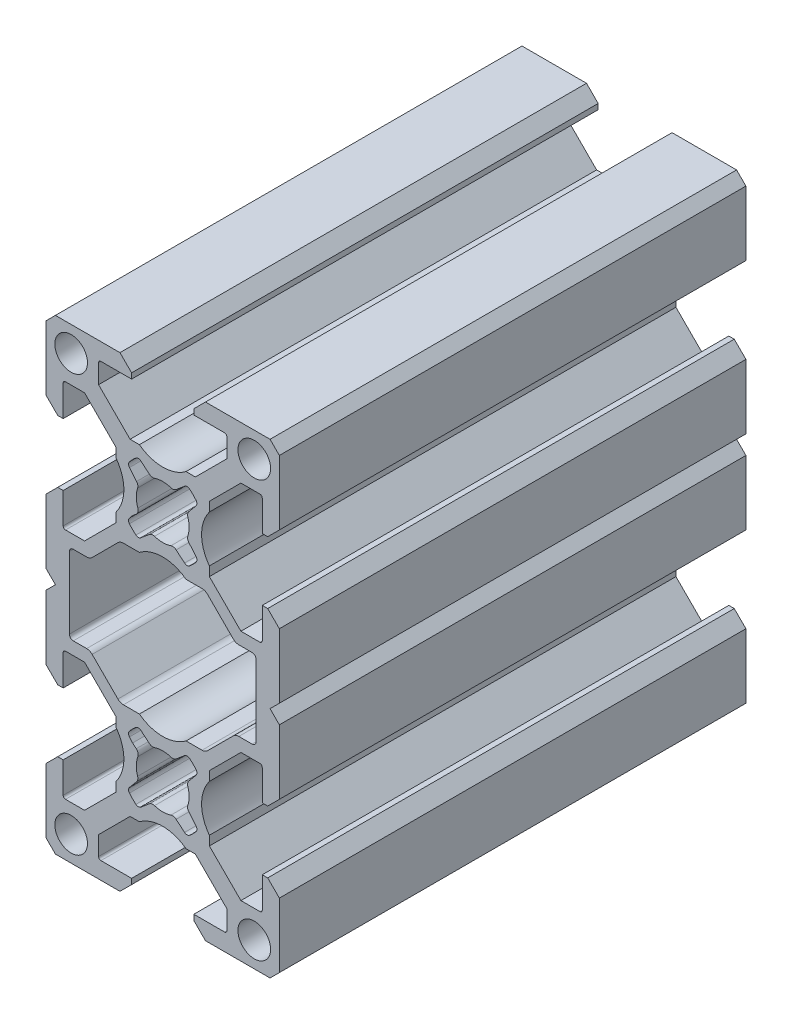
SolidWorks part; units mm, degrees
material "1060-H12"
ref_plane "Спереди" through (0, 0, 0) normal (0, 0, 1) x (1, 0, 0)
ref_plane "Сверху" through (0, 0, 0) normal (0, 1, 0) x (1, 0, 0)
ref_plane "Сбоку" through (0, 0, 0) normal (1, 0, 0) x (0, 0, -1)
sketch "Model" plane through (0, 0, 0) normal (0, 0, 1) x (1, 0, 0)
  line L0 (-6, 19.1969) -> (-6, 15.866)
  line L1 (-10.0531, 6.75) -> (-6, 10.8031)
  line L2 (-12.5, 6.75) -> (-10.0531, 6.75)
  line L3 (-12.8, 11) -> (-12.8, 7.05)
  line L4 (-14.5, 11) -> (-12.8, 11)
  line L5 (-14.5, 10.5) -> (-14.5, 11)
  line L6 (-15, 10.5) -> (-14.5, 10.5)
  line L7 (-1.8557, 11.5271) -> (-2.8145, 10.7226)
  line L8 (-4.2774, 12.1855) -> (-3.4729, 13.1443)
  line L9 (-10.0531, 23.25) -> (-6, 19.1969)
  line L10 (-12.5, 23.25) -> (-10.0531, 23.25)
  line L11 (-12.8, 19) -> (-12.8, 22.95)
  line L12 (-14.5, 19) -> (-12.8, 19)
  line L13 (-14.5, 19.5) -> (-14.5, 19)
  line L14 (-15, 19.5) -> (-14.5, 19.5)
  line L15 (-15, 30) -> (-15, 19.5)
  line L20 (-4.5, 30) -> (-15, 30)
  line L21 (12.8, 19) -> (12.8, 22.95)
  line L22 (14.5, 19) -> (12.8, 19)
  line L23 (14.5, 19.5) -> (14.5, 19)
  line L24 (15, 19.5) -> (14.5, 19.5)
  line L25 (15, 30) -> (15, 19.5)
  line L30 (12.8, 11) -> (12.8, 7.05)
  line L31 (14.5, 11) -> (12.8, 11)
  line L32 (14.5, 10.5) -> (14.5, 11)
  line L33 (15, 10.5) -> (14.5, 10.5)
  line L34 (4.5, 30) -> (15, 30)
  line L35 (-4, 27.8) -> (-7.95, 27.8)
  line L36 (-4, 29.5) -> (-4, 27.8)
  line L37 (-4.5, 29.5) -> (-4, 29.5)
  line L38 (-4.5, 30) -> (-4.5, 29.5)
  line L39 (4, 27.8) -> (7.95, 27.8)
  line L40 (4, 29.5) -> (4, 27.8)
  line L41 (4.5, 29.5) -> (4, 29.5)
  line L42 (4.5, 30) -> (4.5, 29.5)
  line L43 (-1.8557, 18.4729) -> (-2.8145, 19.2774)
  line L44 (-4.2774, 17.8145) -> (-3.4729, 16.8557)
  line L45 (1.8557, 11.5271) -> (2.8145, 10.7226)
  line L46 (4.2774, 12.1855) -> (3.4729, 13.1443)
  line L47 (1.8557, 18.4729) -> (2.8145, 19.2774)
  line L48 (4.2774, 17.8145) -> (3.4729, 16.8557)
  line L49 (-5.5, 15) -> (-6, 15.866)
  line L50 (-6, 14.134) -> (-6, 10.8031)
  line L51 (-5.5, 15) -> (-6, 14.134)
  line L52 (9.0768, 5.3929) -> (5.7626, 8.7071)
  line L53 (-5.0555, 9) -> (5.0555, 9)
  line L54 (-9.0768, 5.3929) -> (-5.7626, 8.7071)
  line L55 (-8.25, 25.0531) -> (-4.1969, 21)
  line L56 (-8.25, 27.5) -> (-8.25, 25.0531)
  line L57 (4.1969, 21) -> (0.866, 21)
  line L58 (8.25, 25.0531) -> (4.1969, 21)
  line L59 (0, 20.5) -> (0.866, 21)
  line L60 (-0.866, 21) -> (-4.1969, 21)
  line L61 (0, 20.5) -> (-0.866, 21)
  line L62 (8.25, 27.5) -> (8.25, 25.0531)
  line L63 (10.0531, 23.25) -> (6, 19.1969)
  line L64 (12.5, 23.25) -> (10.0531, 23.25)
  line L65 (6, 10.8031) -> (6, 14.134)
  line L66 (10.0531, 6.75) -> (6, 10.8031)
  line L67 (5.5, 15) -> (6, 14.134)
  line L68 (6, 15.866) -> (6, 19.1969)
  line L69 (5.5, 15) -> (6, 15.866)
  line L70 (12.5, 6.75) -> (10.0531, 6.75)
  line L71 (-6, -19.1969) -> (-6, -15.866)
  line L72 (-10.0531, -23.25) -> (-6, -19.1969)
  line L73 (-12.5, -23.25) -> (-10.0531, -23.25)
  line L74 (-12.8, -19) -> (-12.8, -22.95)
  line L75 (-14.5, -19) -> (-12.8, -19)
  line L76 (-14.5, -19.5) -> (-14.5, -19)
  line L77 (-15, -19.5) -> (-14.5, -19.5)
  line L78 (-15, -30) -> (-15, -19.5)
  line L83 (-4.5, -30) -> (-15, -30)
  line L84 (12.8, -19) -> (12.8, -22.95)
  line L85 (14.5, -19) -> (12.8, -19)
  line L86 (14.5, -19.5) -> (14.5, -19)
  line L87 (15, -19.5) -> (14.5, -19.5)
  line L88 (15, -30) -> (15, -19.5)
  line L93 (4.5, -30) -> (15, -30)
  line L94 (-4, -27.8) -> (-7.95, -27.8)
  line L95 (-4, -29.5) -> (-4, -27.8)
  line L96 (-4.5, -29.5) -> (-4, -29.5)
  line L97 (-4.5, -30) -> (-4.5, -29.5)
  line L98 (4, -27.8) -> (7.95, -27.8)
  line L99 (4, -29.5) -> (4, -27.8)
  line L100 (4.5, -29.5) -> (4, -29.5)
  line L101 (4.5, -30) -> (4.5, -29.5)
  line L102 (-1.8557, -18.4729) -> (-2.8145, -19.2774)
  line L103 (-4.2774, -17.8145) -> (-3.4729, -16.8557)
  line L104 (1.8557, -18.4729) -> (2.8145, -19.2774)
  line L105 (4.2774, -17.8145) -> (3.4729, -16.8557)
  line L106 (-5.5, -15) -> (-6, -15.866)
  line L107 (-5.5, -15) -> (-6, -14.134)
  line L108 (-8.25, -25.0531) -> (-4.1969, -21)
  line L109 (-8.25, -27.5) -> (-8.25, -25.0531)
  line L110 (4.1969, -21) -> (0.866, -21)
  line L111 (8.25, -25.0531) -> (4.1969, -21)
  line L112 (0, -20.5) -> (0.866, -21)
  line L113 (-0.866, -21) -> (-4.1969, -21)
  line L114 (0, -20.5) -> (-0.866, -21)
  line L115 (8.25, -27.5) -> (8.25, -25.0531)
  line L116 (10.0531, -23.25) -> (6, -19.1969)
  line L117 (12.5, -23.25) -> (10.0531, -23.25)
  line L118 (5.5, -15) -> (6, -14.134)
  line L119 (6, -15.866) -> (6, -19.1969)
  line L120 (5.5, -15) -> (6, -15.866)
  line L121 (-10.0531, -6.75) -> (-6, -10.8031)
  line L122 (-12.5, -6.75) -> (-10.0531, -6.75)
  line L123 (-12.8, -11) -> (-12.8, -7.05)
  line L124 (-14.5, -11) -> (-12.8, -11)
  line L125 (-14.5, -10.5) -> (-14.5, -11)
  line L126 (-15, -10.5) -> (-14.5, -10.5)
  line L127 (-6, -14.134) -> (-6, -10.8031)
  line L128 (-15, 10.5) -> (-15, -10.5)
  line L129 (-1.8557, -11.5271) -> (-2.8145, -10.7226)
  line L130 (-4.2774, -12.1855) -> (-3.4729, -13.1443)
  line L131 (1.8557, -11.5271) -> (2.8145, -10.7226)
  line L132 (4.2774, -12.1855) -> (3.4729, -13.1443)
  line L133 (6, -10.8031) -> (6, -14.134)
  line L134 (10.0531, -6.75) -> (6, -10.8031)
  line L135 (12.8, -11) -> (12.8, -7.05)
  line L136 (14.5, -11) -> (12.8, -11)
  line L137 (14.5, -10.5) -> (14.5, -11)
  line L138 (15, -10.5) -> (14.5, -10.5)
  line L139 (12.5, -6.75) -> (10.0531, -6.75)
  line L140 (15, 10.5) -> (15, -10.5)
  line L141 (9.7839, 5.1) -> (12.35, 5.1)
  line L142 (-9.7839, 5.1) -> (-12.35, 5.1)
  line L143 (-13.35, 4.1) -> (-13.35, -4.1)
  line L144 (13.35, 4.1) -> (13.35, -4.1)
  line L145 (-9.0768, -5.3929) -> (-5.7626, -8.7071)
  line L146 (-9.7839, -5.1) -> (-12.35, -5.1)
  line L147 (-5.0555, -9) -> (5.0555, -9)
  line L148 (9.0768, -5.3929) -> (5.7626, -8.7071)
  line L149 (9.7839, -5.1) -> (12.35, -5.1)
  arc A0 (-3.3914, 16.3495) -> (-3.3914, 13.6505) centre (0, 15) ccw
  arc A1 (-1.3495, 11.6086) -> (1.3495, 11.6086) centre (0, 15) ccw
  arc A2 (-4.2838, 11.5505) -> (-3.4495, 10.7162) centre (0, 15) ccw
  arc A13 (-3.4729, 13.1443) -> (-3.3914, 13.6505) centre (-3.8559, 13.4657) ccw
  arc A14 (-4.2774, 12.1855) -> (-4.2838, 11.5505) centre (-3.8944, 11.8641) ccw
  arc A15 (-3.4495, 10.7162) -> (-2.8145, 10.7226) centre (-3.1359, 11.1056) ccw
  arc A16 (-1.3495, 11.6086) -> (-1.8557, 11.5271) centre (-1.5343, 11.1441) ccw
  arc A17 (-3.4495, 19.2838) -> (-4.2838, 18.4495) centre (0, 15) ccw
  arc A18 (-3.3914, 16.3495) -> (-3.4729, 16.8557) centre (-3.8559, 16.5343) ccw
  arc A19 (-4.2838, 18.4495) -> (-4.2774, 17.8145) centre (-3.8944, 18.1359) ccw
  arc A20 (-2.8145, 19.2774) -> (-3.4495, 19.2838) centre (-3.1359, 18.8944) ccw
  arc A21 (-1.8557, 18.4729) -> (-1.3495, 18.3914) centre (-1.5343, 18.8559) ccw
  arc A22 (3.3914, 13.6505) -> (3.3914, 16.3495) centre (0, 15) ccw
  arc A23 (3.4495, 10.7162) -> (4.2838, 11.5505) centre (0, 15) ccw
  arc A24 (3.3914, 13.6505) -> (3.4729, 13.1443) centre (3.8559, 13.4657) ccw
  arc A25 (4.2838, 11.5505) -> (4.2774, 12.1855) centre (3.8944, 11.8641) ccw
  arc A26 (2.8145, 10.7226) -> (3.4495, 10.7162) centre (3.1359, 11.1056) ccw
  arc A27 (1.8557, 11.5271) -> (1.3495, 11.6086) centre (1.5343, 11.1441) ccw
  arc A28 (4.2838, 18.4495) -> (3.4495, 19.2838) centre (0, 15) ccw
  arc A29 (3.4729, 16.8557) -> (3.3914, 16.3495) centre (3.8559, 16.5343) ccw
  arc A30 (4.2774, 17.8145) -> (4.2838, 18.4495) centre (3.8944, 18.1359) ccw
  arc A31 (3.4495, 19.2838) -> (2.8145, 19.2774) centre (3.1359, 18.8944) ccw
  arc A32 (1.3495, 18.3914) -> (1.8557, 18.4729) centre (1.5343, 18.8559) ccw
  arc A33 (1.3495, 18.3914) -> (-1.3495, 18.3914) centre (0, 15) ccw
  arc A34 (-12.8, 7.05) -> (-12.5, 6.75) centre (-12.5, 7.05) ccw
  arc A35 (-12.5, 23.25) -> (-12.8, 22.95) centre (-12.5, 22.95) ccw
  arc A36 (-7.95, 27.8) -> (-8.25, 27.5) centre (-7.95, 27.5) ccw
  arc A37 (8.25, 27.5) -> (7.95, 27.8) centre (7.95, 27.5) ccw
  arc A38 (12.8, 22.95) -> (12.5, 23.25) centre (12.5, 22.95) ccw
  arc A39 (12.5, 6.75) -> (12.8, 7.05) centre (12.5, 7.05) ccw
  arc A40 (-3.3914, -13.6505) -> (-3.3914, -16.3495) centre (0, -15) ccw
  arc A51 (-4.2838, -18.4495) -> (-3.4495, -19.2838) centre (0, -15) ccw
  arc A52 (-3.4729, -16.8557) -> (-3.3914, -16.3495) centre (-3.8559, -16.5343) ccw
  arc A53 (-4.2774, -17.8145) -> (-4.2838, -18.4495) centre (-3.8944, -18.1359) ccw
  arc A54 (-3.4495, -19.2838) -> (-2.8145, -19.2774) centre (-3.1359, -18.8944) ccw
  arc A55 (-1.3495, -18.3914) -> (-1.8557, -18.4729) centre (-1.5343, -18.8559) ccw
  arc A56 (3.3914, -16.3495) -> (3.3914, -13.6505) centre (0, -15) ccw
  arc A57 (3.4495, -19.2838) -> (4.2838, -18.4495) centre (0, -15) ccw
  arc A58 (3.3914, -16.3495) -> (3.4729, -16.8557) centre (3.8559, -16.5343) ccw
  arc A59 (4.2838, -18.4495) -> (4.2774, -17.8145) centre (3.8944, -18.1359) ccw
  arc A60 (2.8145, -19.2774) -> (3.4495, -19.2838) centre (3.1359, -18.8944) ccw
  arc A61 (1.8557, -18.4729) -> (1.3495, -18.3914) centre (1.5343, -18.8559) ccw
  arc A62 (-1.3495, -18.3914) -> (1.3495, -18.3914) centre (0, -15) ccw
  arc A63 (-12.8, -22.95) -> (-12.5, -23.25) centre (-12.5, -22.95) ccw
  arc A64 (-8.25, -27.5) -> (-7.95, -27.8) centre (-7.95, -27.5) ccw
  arc A65 (7.95, -27.8) -> (8.25, -27.5) centre (7.95, -27.5) ccw
  arc A66 (12.5, -23.25) -> (12.8, -22.95) centre (12.5, -22.95) ccw
  arc A67 (-4.2838, -11.5505) -> (-4.2774, -12.1855) centre (-3.8944, -11.8641) ccw
  arc A68 (-12.5, -6.75) -> (-12.8, -7.05) centre (-12.5, -7.05) ccw
  arc A69 (1.3495, -11.6086) -> (-1.3495, -11.6086) centre (0, -15) ccw
  arc A70 (-3.4495, -10.7162) -> (-4.2838, -11.5505) centre (0, -15) ccw
  arc A71 (-3.3914, -13.6505) -> (-3.4729, -13.1443) centre (-3.8559, -13.4657) ccw
  arc A72 (-2.8145, -10.7226) -> (-3.4495, -10.7162) centre (-3.1359, -11.1056) ccw
  arc A73 (-1.8557, -11.5271) -> (-1.3495, -11.6086) centre (-1.5343, -11.1441) ccw
  arc A74 (4.2838, -11.5505) -> (3.4495, -10.7162) centre (0, -15) ccw
  arc A75 (3.4729, -13.1443) -> (3.3914, -13.6505) centre (3.8559, -13.4657) ccw
  arc A76 (4.2774, -12.1855) -> (4.2838, -11.5505) centre (3.8944, -11.8641) ccw
  arc A77 (3.4495, -10.7162) -> (2.8145, -10.7226) centre (3.1359, -11.1056) ccw
  arc A78 (1.3495, -11.6086) -> (1.8557, -11.5271) centre (1.5343, -11.1441) ccw
  arc A79 (12.8, -7.05) -> (12.5, -6.75) centre (12.5, -7.05) ccw
  arc A80 (-12.35, 5.1) -> (-13.35, 4.1) centre (-12.35, 4.1) ccw
  arc A81 (-13.35, -4.1) -> (-12.35, -5.1) centre (-12.35, -4.1) ccw
  arc A82 (12.35, -5.1) -> (13.35, -4.1) centre (12.35, -4.1) ccw
  arc A83 (13.35, 4.1) -> (12.35, 5.1) centre (12.35, 4.1) ccw
  arc A84 (-9.7839, 5.1) -> (-9.0768, 5.3929) centre (-9.7839, 6.1) ccw
  arc A85 (-5.0555, 9) -> (-5.7626, 8.7071) centre (-5.0555, 8) ccw
  arc A86 (5.7626, 8.7071) -> (5.0555, 9) centre (5.0555, 8) ccw
  arc A87 (9.0768, 5.3929) -> (9.7839, 5.1) centre (9.7839, 6.1) ccw
  arc A88 (9.7839, -5.1) -> (9.0768, -5.3929) centre (9.7839, -6.1) ccw
  arc A89 (5.0555, -9) -> (5.7626, -8.7071) centre (5.0555, -8) ccw
  arc A90 (-5.7626, -8.7071) -> (-5.0555, -9) centre (-5.0555, -8) ccw
  arc A91 (-9.0768, -5.3929) -> (-9.7839, -5.1) centre (-9.7839, -6.1) ccw
  point P19 (-11.775, -26.775)
  point P21 (11.775, -26.775)
  point P34 (-11.775, 26.775)
  point P100 (11.775, 26.775)
extrude "Бобышка-Вытянуть1" add sketch "Model" along normal blind 60
chamfer "Фаска1" distance 1.2 angle 45 4 edges at (-15, -30, 30) (15, -30, 30) (-15, 30, 30) (15, 30, 30)
sketch "Эскиз2" plane through (0, 0, 60) normal (0, 0, 1) x (1, 0, 0)
  line L0 (-15, 1.2) -> (-13.8, 0)
  line L1 (-15, 10.5) -> (-15, -10.5) construction
  line L2 (-13.8, 0) -> (-15, -1.2)
  line L3 (15, 1.2) -> (13.8, 0)
  line L4 (15, -10.5) -> (15, 10.5) construction
  line L5 (13.8, 0) -> (15, -1.2)
  line L6 (-15, 0) -> (15, 0) construction
  line L7 (-15, 1.2) -> (-15, -1.2)
  line L8 (15, 1.2) -> (15, -1.2)
  line L9 (-4, 28.5) -> (-5.5, 30)
  line L10 (-4, 29.5) -> (-4, 27.8) construction
  line L11 (-4.5, 30) -> (-15, 30) construction
  line L12 (-5.5, 30) -> (5.5, 30)
  line L13 (4.5, 30) -> (15, 30) construction
  line L14 (5.5, 30) -> (4, 28.5)
  line L15 (4, 29.5) -> (4, 27.8) construction
  line L16 (4, 28.5) -> (-4, 28.5)
  line L17 (-13.8, 30) -> (-15, 28.8) construction
  line L18 (4, -28.5) -> (-4, -28.5)
  line L19 (5.5, -30) -> (4, -28.5)
  line L20 (-5.5, -30) -> (5.5, -30)
  line L21 (-4, -28.5) -> (-5.5, -30)
  line L22 (-15, 20.5) -> (-15, 9.5)
  line L23 (-15, 30) -> (-15, 19.5) construction
  line L24 (-15, 10.5) -> (-15, -10.5) construction
  line L25 (-15, 9.5) -> (-13.5, 11)
  line L26 (-14.5, 11) -> (-12.8, 11) construction
  line L27 (-13.5, 11) -> (-13.5, 19)
  line L28 (-13.5, 19) -> (-15, 20.5)
  line L29 (-15, -28.8) -> (-13.8, -30) construction
  line L30 (-14.5, 19) -> (-12.8, 19) construction
  line L31 (-15, -20.5) -> (-13.5, -19)
  line L32 (-13.5, -19) -> (-13.5, -11)
  line L33 (-15, -9.5) -> (-15, -20.5)
  line L34 (-13.5, -11) -> (-15, -9.5)
  line L35 (-14.5, -19) -> (-12.8, -19) construction
  line L36 (-14.5, -11) -> (-12.8, -11) construction
  line L37 (0, 0) -> (0, -6.8529) construction
  line L38 (13.5, 19) -> (15, 20.5)
  line L39 (13.5, 11) -> (13.5, 19)
  line L40 (15, 9.5) -> (13.5, 11)
  line L41 (15, 20.5) -> (15, 9.5)
  line L42 (13.5, -11) -> (15, -9.5)
  line L43 (15, -9.5) -> (15, -20.5)
  line L44 (13.5, -19) -> (13.5, -11)
  line L45 (15, -20.5) -> (13.5, -19)
  dimension "D1" = 1.5
extrude "Вырез-Вытянуть1" cut sketch "Эскиз2" against normal through all
hole_wizard "Отверстие с зазором M41" positions "Эскиз4" profile "Эскиз5" hole size "M4" standard "DIN" end condition through all
sketch "Эскиз4" plane through (0, 0, 60) normal (0, 0, 1) x (1, 0, 0)
  point P0 (-11.775, 26.775)
  point P3 (11.775, 26.775)
  point P6 (11.775, -26.775)
  point P9 (-11.775, -26.775)
sketch "Эскиз5" plane through (-11.775, 26.775, 60) normal (1, 0, 0) x (0, -1, 0)
  line L0 (0, 0) -> (0, 60)
  line L1 (0, 60) -> (2.1, 60)
  line L2 (2.1, 60) -> (2.1, 0)
  line L5 (2.1, 0) -> (0, 0)
  line L11 (0, -6.35) -> (0, 107.95) construction
  dimension "Диаметр сквозного отверстия" = 4.2
  dimension "Глубина сквозного отверстия" = 60
sketch "Эскиз6" plane through (0, 0, 60) normal (0, 0, 1) x (1, 0, 0)
  line L0 (15, -9.5) -> (15, -1.2) construction
  line L1 (-12, 5.1) -> (-13.8, 5.1)
  line L2 (-12, 5.1) -> (-12, -5.1)
  line L3 (-12, -5.1) -> (-13.8, -5.1)
  line L4 (-13.8, 5.1) -> (-13.8, -5.1)
  line L5 (13.8, 5.1) -> (12, 5.1)
  line L6 (13.8, 5.1) -> (13.8, -5.1)
  line L7 (13.8, -5.1) -> (12, -5.1)
  line L8 (12, 5.1) -> (12, -5.1)
  line L9 (-15, -1.2) -> (-15, -9.5) construction
  line L10 (-9.7839, 5.1) -> (-12.35, 5.1) construction
  line L11 (-12.35, -5.1) -> (-9.7839, -5.1) construction
  line L12 (9.7839, -5.1) -> (12.35, -5.1) construction
  line L13 (12.35, 5.1) -> (9.7839, 5.1) construction
  dimension "D1" = 3
  dimension "D2" = 3
extrude "Бобышка-Вытянуть2" add sketch "Эскиз6" against normal up to surface (60 mm away) up to face at (-9.675, 26.775, 0)
fillet "Скругление1" radius 0.5 4 edges at (-12, -5.1, 30) (-12, 5.1, 30) (12, -5.1, 30) (12, 5.1, 30)
sketch "Эскиз7" plane through (0, 0, 0) normal (0, 0, -1) x (-1, 0, 0)
  line L9 (0, -15) -> (-10, -15) construction
  line L10 (0, -15) -> (10, -15) construction
  line L11 (0, -25) -> (0, -15) construction
  line L12 (0, 0) -> (5.8948, 0) construction
  line L13 (4.6648, -26.8) -> (-4.6648, -26.8)
  line L14 (12.8, -11) -> (12.8, -7.05) construction
  line L15 (0, 25) -> (0, 15) construction
  line L16 (0, -5) -> (0, -15) construction
  line L17 (11.8, -10.3352) -> (11.8, -19.6648)
  line L18 (-11.8, -10.3352) -> (-11.8, -19.6648)
  line L19 (0, 15) -> (10, 15) construction
  line L20 (0, 15) -> (-10, 15) construction
  line L21 (-11.8, 10.3352) -> (-11.8, 19.6648)
  line L22 (11.8, 10.3352) -> (11.8, 19.6648)
  line L23 (4.6648, 26.8) -> (-4.6648, 26.8)
  line L24 (2.1794, 0.5) -> (-2.1794, 0.5)
  line L25 (-2.1794, -0.5) -> (2.1794, -0.5)
  arc A0 (4.6648, 26.8) -> (-4.6648, 26.8) centre (0, 25) cw
  arc A1 (-11.8, 19.6648) -> (-11.8, 10.3352) centre (-10, 15) cw
  arc A2 (11.8, 10.3352) -> (11.8, 19.6648) centre (10, 15) cw
  arc A3 (-2.1794, -0.5) -> (2.1794, -0.5) centre (0, -5) ccw
  arc A4 (11.8, -10.3352) -> (11.8, -19.6648) centre (10, -15) ccw
  arc A5 (-2.1794, 0.5) -> (2.1794, 0.5) centre (0, 5) cw
  arc A6 (-11.8, -19.6648) -> (-11.8, -10.3352) centre (-10, -15) ccw
  arc A8 (4.6648, -26.8) -> (-4.6648, -26.8) centre (0, -25) ccw
  dimension "D1" = 10
  dimension "D2" = 10
  dimension "D3" = 1
  dimension "D4" = 1
extrude "Снижение массы" cut sketch "Эскиз7" against normal through all
sketch "Эскиз9" plane through (0, 0, 60) normal (0, 0, 1) x (1, 0, 0)
  line L0 (2.3351, -11.1248) -> (1.7226, -11.6388)
  line L1 (2.8145, -10.7226) -> (1.8557, -11.5271) construction
  line L2 (-2.3351, -11.1248) -> (-1.7226, -11.6388)
  line L3 (-1.8557, -11.5271) -> (-2.8145, -10.7226) construction
  line L4 (-3.8752, -12.6649) -> (-3.4027, -13.0613)
  line L5 (-4.2774, -12.1855) -> (-3.4729, -13.1443) construction
  line L6 (-3.8752, -17.3351) -> (-3.3612, -16.7226)
  line L7 (-3.4729, -16.8557) -> (-4.2774, -17.8145) construction
  line L8 (-2.3351, -18.8752) -> (-1.7226, -18.3612)
  line L9 (-2.8145, -19.2774) -> (-1.8557, -18.4729) construction
  line L10 (2.3351, -18.8752) -> (1.7226, -18.3612)
  line L11 (1.8557, -18.4729) -> (2.8145, -19.2774) construction
  line L12 (3.8752, -17.3351) -> (3.3612, -16.7226)
  line L13 (4.2774, -17.8145) -> (3.4729, -16.8557) construction
  line L14 (3.8752, -12.6649) -> (3.3612, -13.2774)
  line L15 (3.4729, -13.1443) -> (4.2774, -12.1855) construction
  line L16 (-3.8752, -12.6649) -> (-3.8752, -17.3351)
  line L17 (-2.3351, -18.8752) -> (2.3351, -18.8752)
  line L18 (3.8752, -17.3351) -> (3.8752, -12.6649)
  line L19 (2.3351, -11.1248) -> (-2.3351, -11.1248)
  line L20 (0, 0) -> (6.1953, 0) construction
  line L21 (2.3351, 11.1248) -> (-2.3351, 11.1248)
  line L22 (3.8752, 17.3351) -> (3.8752, 12.6649)
  line L23 (-2.3351, 18.8752) -> (2.3351, 18.8752)
  line L24 (-3.8752, 12.6649) -> (-3.8752, 17.3351)
  line L25 (3.8752, 12.6649) -> (3.3612, 13.2774)
  line L26 (3.8752, 17.3351) -> (3.3612, 16.7226)
  line L27 (2.3351, 18.8752) -> (1.7226, 18.3612)
  line L28 (-2.3351, 18.8752) -> (-1.7226, 18.3612)
  line L29 (-3.8752, 17.3351) -> (-3.3612, 16.7226)
  line L30 (-3.8752, 12.6649) -> (-3.4027, 13.0613)
  line L31 (-2.3351, 11.1248) -> (-1.7226, 11.6388)
  line L32 (2.3351, 11.1248) -> (1.7226, 11.6388)
  arc A0 (-1.0554, -18.232) -> (1.0554, -18.232) centre (0, -15) ccw
  arc A1 (-3.1949, -13.837) -> (-3.232, -16.0554) centre (0, -15) ccw
  arc A2 (1.0554, -11.768) -> (-1.0554, -11.768) centre (0, -15) ccw
  arc A3 (3.232, -16.0554) -> (3.232, -13.9446) centre (0, -15) ccw
  arc A4 (3.232, 16.0554) -> (3.232, 13.9446) centre (0, 15) cw
  arc A5 (1.0554, 11.768) -> (-1.0554, 11.768) centre (0, 15) cw
  arc A6 (-3.1949, 13.837) -> (-3.232, 16.0554) centre (0, 15) cw
  arc A7 (-1.0554, 18.232) -> (1.0554, 18.232) centre (0, 15) cw
  arc A8 (-3.4027, -13.0613) -> (-3.1949, -13.837) centre (-3.8527, -13.5975) cw
  arc A9 (-3.3612, -16.7226) -> (-3.232, -16.0554) centre (-3.8975, -16.2727) ccw
  arc A10 (-1.7226, -18.3612) -> (-1.0554, -18.232) centre (-1.2727, -18.8975) cw
  arc A11 (1.7226, -18.3612) -> (1.0554, -18.232) centre (1.2727, -18.8975) ccw
  arc A12 (3.3612, -16.7226) -> (3.232, -16.0554) centre (3.8975, -16.2727) cw
  arc A13 (3.3612, -13.2774) -> (3.232, -13.9446) centre (3.8975, -13.7273) ccw
  arc A14 (1.7226, -11.6388) -> (1.0554, -11.768) centre (1.2727, -11.1025) cw
  arc A15 (-1.7226, -11.6388) -> (-1.0554, -11.768) centre (-1.2727, -11.1025) ccw
  arc A16 (-1.0554, 11.768) -> (-1.7226, 11.6388) centre (-1.2727, 11.1025) ccw
  arc A17 (1.0554, 11.768) -> (1.7226, 11.6388) centre (1.2727, 11.1025) cw
  arc A18 (3.232, 13.9446) -> (3.3612, 13.2774) centre (3.8975, 13.7273) ccw
  arc A19 (3.232, 16.0554) -> (3.3612, 16.7226) centre (3.8975, 16.2727) cw
  arc A20 (1.0554, 18.232) -> (1.7226, 18.3612) centre (1.2727, 18.8975) ccw
  arc A21 (-1.0554, 18.232) -> (-1.7226, 18.3612) centre (-1.2727, 18.8975) cw
  arc A22 (-3.1949, 13.837) -> (-3.4027, 13.0613) centre (-3.8527, 13.5975) cw
  arc A23 (-3.232, 16.0554) -> (-3.3612, 16.7226) centre (-3.8975, 16.2727) ccw
  point P56 (-2.9997, -13.3995)
  point P59 (-3.0956, -16.4061)
  point P62 (-1.4061, -18.0956)
  point P65 (1.4061, -18.0956)
  point P68 (3.0956, -16.4061)
  point P71 (3.0956, -13.5939)
  point P74 (1.4061, -11.9044)
  point P77 (-1.4061, -11.9044)
  point P80 (-1.4061, 11.9044)
  point P83 (1.4061, 11.9044)
  point P86 (3.0956, 13.5939)
  point P89 (3.0956, 16.4061)
  point P92 (1.4061, 18.0956)
  point P95 (-1.4061, 18.0956)
  point P98 (-2.9997, 13.3995)
  point P101 (-3.0956, 16.4061)
  dimension "D1" = 6.8
  dimension "D2" = 0.7
extrude "Бобышка-Вытянуть3" add sketch "Эскиз9" against normal up to surface (60 mm away) up to face at (0, 0, 0)
